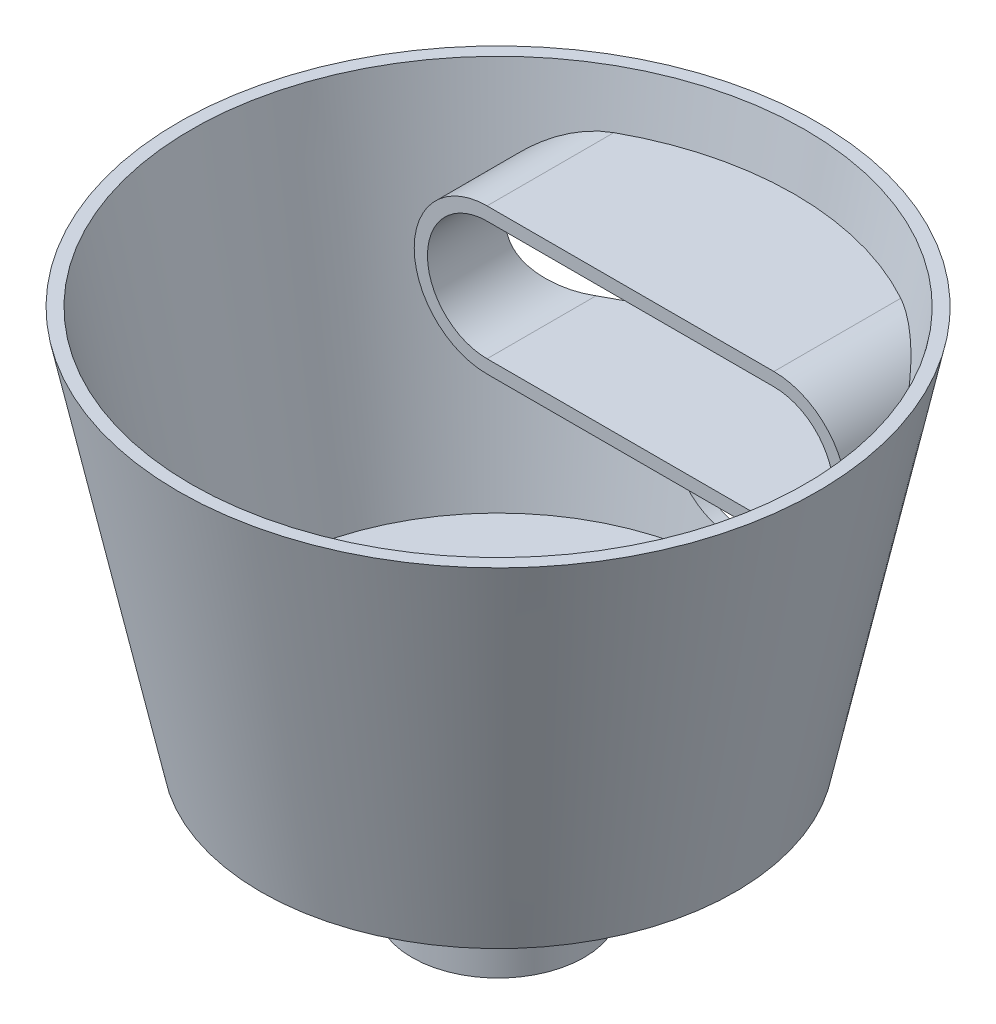
SolidWorks part; units mm, degrees
material "PLA"
ref_plane "Front Plane" through (0, 0, 0) normal (0, 0, 1) x (1, 0, 0)
ref_plane "Top Plane" through (0, 0, 0) normal (0, 1, 0) x (1, 0, 0)
ref_plane "Right Plane" through (0, 0, 0) normal (1, 0, 0) x (0, 0, -1)
sketch "Sketch1" plane through (0, 0, 0) normal (0, 1, 0) x (1, 0, 0)
  circle A0 centre (0, 0) radius 75
  dimension "D1" = 150
extrude "Boss-Extrude1" add sketch "Sketch1" against normal blind 100 draft 12
ref_plane "Plane1" through (0, -10, 0) normal (0, 1, 0) x (1, 0, 0)
sketch "Sketch3" plane through (0, -10, 0) normal (0, 1, 0) x (1, 0, 0)
  circle A0 centre (0, 0) radius 70
  dimension "D1" = 140
extrude "Cut-Extrude1" cut sketch "Sketch3" against normal blind 80 draft 12
fillet "Fillet1" radius 10 1 edges at (0, 0, 75)
sketch "Sketch4" plane through (0, 0, 0) normal (0, 0, 1) x (1, 0, 0)
  line L0 (-15, -70) -> (15, -70)
  line L1 (-32.5, -26.5) -> (32.5, -26.5)
  line L2 (-32.5, -53.5) -> (32.5, -53.5)
  line L3 (-46, -40) -> (46, -40) construction
  arc A0 (-32.5, -26.5) -> (-32.5, -53.5) centre (-32.5, -40) ccw
  arc A1 (32.5, -53.5) -> (32.5, -26.5) centre (32.5, -40) ccw
  arc A2 (-15, -70) -> (15, -70) centre (0, -70) ccw
  dimension "D1" = 27
  dimension "D2" = 65
  dimension "D3" = 32.5
  dimension "D4" = 40
  dimension "D5" = 30
  dimension "D6" = 70
extrude "Cut-Extrude2" cut sketch "Sketch4" against normal blind 90
sketch "Sketch5" plane through (0, -100, 0) normal (0, -1, 0) x (1, 0, 0)
  circle A0 centre (0, 0) radius 19.5
  circle A1 centre (0, 0) radius 17.5
  dimension "D1" = 39
  dimension "D2" = 35
extrude "Boss-Extrude2" add sketch "Sketch5" along normal blind 30
sketch "Sketch6" plane through (0, -100, 0) normal (0, -1, 0) x (1, 0, 0)
  circle A1 centre (0, 0) radius 17.5
  circle A2 centre (0, 0) radius 17.5
  dimension "D1" = 0
extrude "Cut-Extrude3" cut sketch "Sketch6" against normal blind 30
ref_plane "Plane6" through (0, 0, -30) normal (0, 0, 1) x (1, 0, 0)
sketch "Sketch16" plane through (0, 0, -30) normal (0, 0, 1) x (1, 0, 0)
  line L0 (32.5, -40) -> (-32.5, -40) construction
  line L1 (32.5, -53.5) -> (-32.5, -53.5)
  line L2 (32.5, -26.5) -> (-32.5, -26.5)
  line L3 (32.5, -40) -> (-32.5, -40) construction
  line L4 (32.5, -56.5) -> (-32.5, -56.5)
  line L5 (32.5, -23.5) -> (-32.5, -23.5)
  arc A0 (32.5, -53.5) -> (32.5, -26.5) centre (32.5, -40) ccw
  arc A1 (-32.5, -26.5) -> (-32.5, -53.5) centre (-32.5, -40) ccw
  arc A2 (32.5, -56.5) -> (32.5, -23.5) centre (32.5, -40) ccw
  arc A3 (-32.5, -23.5) -> (-32.5, -56.5) centre (-32.5, -40) ccw
  point P2 (0, -40)
  point P7 (0, -40)
  dimension "D2" = 13.5
  dimension "D3" = 3
  dimension "D1" = 65
  dimension "D4" = 32.5
  dimension "D5" = 40
extrude "Boss-Extrude7" add sketch "Sketch16" against normal up to surface (21.33 mm away)
ref_plane "Plane7" through (0, -12.0791, 0) normal (0, 1, 0) x (1, 0, 0)
sketch "Sketch17" plane through (0, -12.0791, 0) normal (0, 1, 0) x (1, 0, 0)
  circle A2 centre (0, 0) radius 73.5
  dimension "D1" = 147
extrude "Cut-Extrude4" cut sketch "Sketch17" along normal blind 25
sketch "Sketch18" plane through (0, 0, 0) normal (1, 0, 0) x (0, 0, -1)
  line L0 (0, -130) -> (0, -100) construction
  line L1 (-19.5, -130) -> (19.5, -130) construction
  line L2 (-19.5, -100) -> (19.5, -100) construction
  circle A0 centre (0, -115) radius 3
  dimension "D1" = 6
extrude "Cut-Extrude5" cut sketch "Sketch18" against normal through all both and the other way through all
